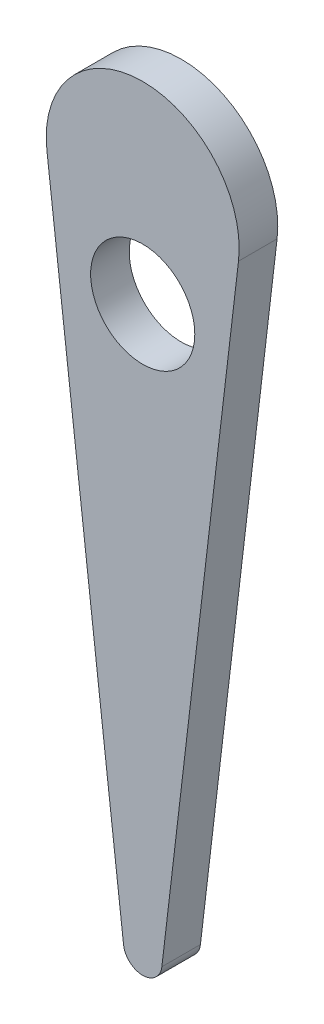
SolidWorks part; units mm, degrees
ref_plane "Ön Düzlem" through (0, 0, 0) normal (0, 0, 1) x (1, 0, 0)
ref_plane "Üst Düzlem" through (0, 0, 0) normal (0, 1, 0) x (1, 0, 0)
ref_plane "Sağ Düzlem" through (0, 0, 0) normal (1, 0, 0) x (0, 0, -1)
sketch "Çizim1" plane through (0, 0, 0) normal (0, 0, 1) x (1, 0, 0)
  line L1 (24.8277, 22.0701) -> (4.9655, -146.2381)
  line L2 (-24.8277, 22.0701) -> (-4.9655, -146.2381)
  line L3 (0, 25) -> (0, -145.6521) construction
  circle A0 centre (0, 25) radius 25 construction
  circle A1 centre (0, -145.6521) radius 5 construction
  circle A2 centre (0, 0) radius 13.5
  arc A3 (-24.8277, 22.0701) -> (24.8277, 22.0701) centre (0, 25) cw
  arc A4 (-4.9655, -146.2381) -> (4.9655, -146.2381) centre (0, -145.6521) ccw
  dimension "D1" = 27
  dimension "D2" = 170.6521
  dimension "D3" = 50
  dimension "D5" = 10
extrude "Yükseklik-Ekstrüzyon1" add sketch "Çizim1" along normal blind 10
